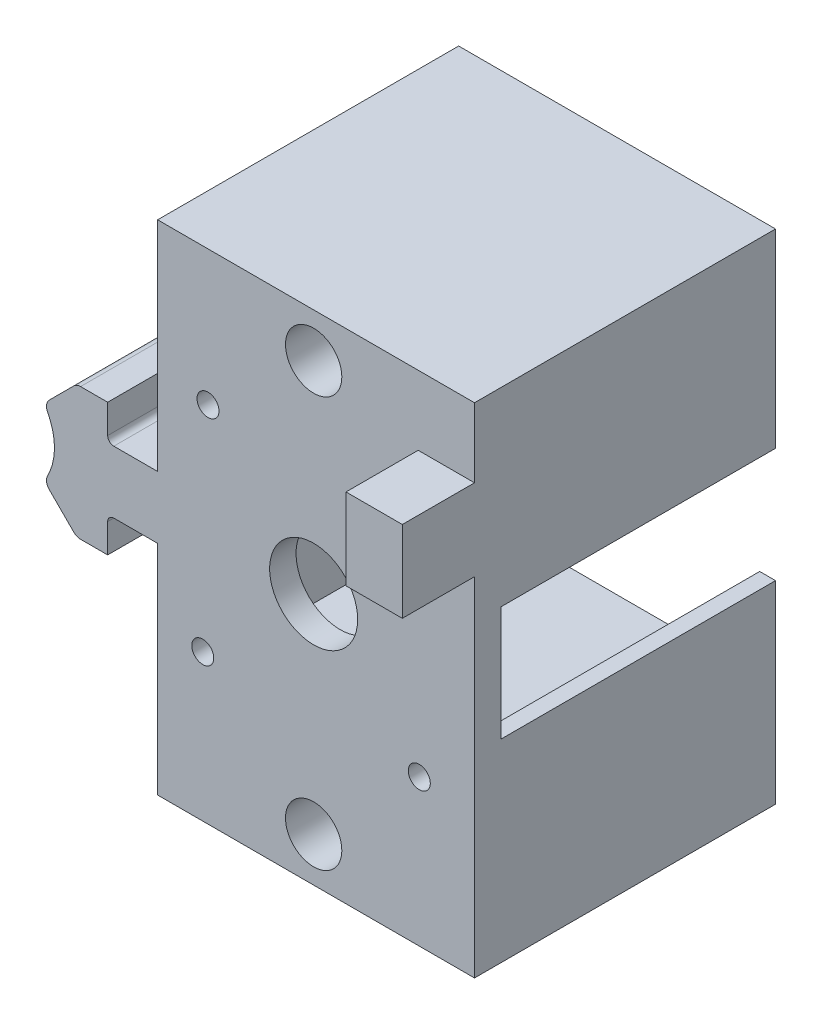
SolidWorks part; units mm, degrees
ref_plane "Front Plane" through (0, 0, 0) normal (0, 0, 1) x (1, 0, 0)
ref_plane "Top Plane" through (0, 0, 0) normal (0, 1, 0) x (1, 0, 0)
ref_plane "Right Plane" through (0, 0, 0) normal (1, 0, 0) x (0, 0, -1)
sketch "Sketch2" plane through (0, 0, 816.4924) normal (0, 0, 1) x (1, 0, 0)
  line L0 (35.7501, 34.0976) -> (35.7501, 33.2853)
  line L27 (48.1133, 38.1834) -> (50.6533, 38.1834)
  line L28 (50.6533, 38.1834) -> (50.6533, 56.9324)
  line L29 (50.6533, 56.9324) -> (52.6853, 56.9324)
  line L30 (52.6853, 56.9324) -> (52.6853, 10.4504)
  line L31 (52.6853, 10.4504) -> (50.6533, 10.4504)
  line L32 (50.6533, 10.4504) -> (50.6533, 29.1994)
  line L33 (50.6533, 29.1994) -> (48.1133, 29.1994)
  line L37 (44.3288, 29.1994) -> (48.1133, 29.1994)
  line L38 (43.4438, 24.1494) -> (43.4438, 28.3144)
  line L39 (39.5326, 24.1494) -> (43.4438, 24.1494)
  line L40 (35.016, 28.0957) -> (38.5589, 24.5527)
  line L41 (35.4657, 33.6914) -> (35.7501, 33.2853)
  line L42 (35.7501, 34.0976) -> (35.4657, 33.6914)
  line L43 (38.5589, 42.8301) -> (35.016, 39.2872)
  line L44 (43.4438, 43.2334) -> (39.5326, 43.2334)
  line L45 (43.4438, 39.0684) -> (43.4438, 43.2334)
  line L46 (48.1133, 38.1834) -> (44.3288, 38.1834)
  line L47 (44.3288, 29.1994) -> (48.1133, 29.1994)
  line L48 (43.4438, 24.1494) -> (43.4438, 28.3144)
  line L49 (39.5326, 24.1494) -> (43.4438, 24.1494)
  line L50 (35.016, 28.0957) -> (38.5589, 24.5527)
  line L53 (38.5589, 42.8301) -> (35.016, 39.2872)
  line L54 (43.4438, 43.2334) -> (39.5326, 43.2334)
  line L55 (43.4438, 39.0684) -> (43.4438, 43.2334)
  line L56 (48.1133, 38.1834) -> (44.3288, 38.1834)
  arc A38 (44.3288, 29.1994) -> (43.4438, 28.3144) centre (44.3288, 28.3144) ccw
  arc A39 (38.5589, 24.5527) -> (39.5326, 24.1494) centre (39.5326, 25.5264) ccw
  arc A40 (34.7724, 29.7132) -> (35.016, 28.0957) centre (35.9896, 29.0694) ccw
  arc A41 (34.7724, 29.7132) -> (35.7501, 33.2853) centre (27.2518, 33.6914) ccw
  arc A42 (35.7501, 34.0976) -> (34.7724, 37.6696) centre (27.2518, 33.6914) ccw
  arc A43 (35.016, 39.2872) -> (34.7724, 37.6696) centre (35.9896, 38.3135) ccw
  arc A44 (39.5326, 43.2334) -> (38.5589, 42.8301) centre (39.5326, 41.8564) ccw
  arc A45 (43.4438, 39.0684) -> (44.3288, 38.1834) centre (44.3288, 39.0684) ccw
  arc A46 (44.3288, 29.1994) -> (43.4438, 28.3144) centre (44.3288, 28.3144) ccw
  arc A47 (38.5589, 24.5527) -> (39.5326, 24.1494) centre (39.5326, 25.5264) ccw
  arc A48 (34.7724, 29.7132) -> (35.016, 28.0957) centre (35.9896, 29.0694) ccw
  arc A49 (34.7724, 29.7132) -> (35.7501, 33.2853) centre (27.2518, 33.6914) ccw
  arc A50 (35.7501, 34.0976) -> (34.7724, 37.6696) centre (27.2518, 33.6914) ccw
  arc A51 (35.016, 39.2872) -> (34.7724, 37.6696) centre (35.9896, 38.3135) ccw
  arc A52 (39.5326, 43.2334) -> (38.5589, 42.8301) centre (39.5326, 41.8564) ccw
  arc A53 (43.4438, 39.0684) -> (44.3288, 38.1834) centre (44.3288, 39.0684) ccw
  dimension "D2" = 46.482
  dimension "D3" = 2.032
  dimension "D4" = 2.54
  dimension "D1" = 0.508
extrude "Boss-Extrude1" add sketch "Sketch2" along normal blind 43.434
sketch "Sketch3" plane through (52.6853, 0, 0) normal (1, 0, 0) x (0, 0, -1)
  line L0 (-859.9264, 10.4504) -> (-816.4924, 10.4504) construction
  line L1 (-859.9264, 56.9324) -> (-856.1164, 56.9324)
  line L2 (-859.9264, 56.9324) -> (-859.9264, 10.4504)
  line L3 (-859.9264, 10.4504) -> (-856.1164, 10.4504)
  line L4 (-856.1164, 56.9324) -> (-856.1164, 10.4504)
  dimension "D1" = 3.81
extrude "Boss-Extrude2" add sketch "Sketch3" along normal blind 43.688
sketch "Sketch8" plane through (0, 0, 856.1164) normal (0, 0, -1) x (-1, 0, 0)
  line L0 (-52.6853, 10.4504) -> (-52.6853, 56.9324) construction
  line L1 (-96.3733, 56.9324) -> (-52.6853, 56.9324)
  line L2 (-96.3733, 56.9324) -> (-96.3733, 54.9004)
  line L3 (-94.0873, 54.9004) -> (-52.6853, 54.9004)
  line L4 (-52.6853, 56.9324) -> (-52.6853, 54.9004)
  line L6 (-96.3733, 10.4504) -> (-52.6853, 10.4504)
  line L7 (-96.3733, 10.4504) -> (-96.3733, 12.4824)
  line L8 (-94.0873, 12.4824) -> (-52.6853, 12.4824)
  line L9 (-52.6853, 10.4504) -> (-52.6853, 12.4824)
  line L11 (-96.3733, 54.9004) -> (-96.3733, 42.2204)
  line L12 (-96.3733, 42.2204) -> (-94.0873, 42.2204)
  line L13 (-94.0873, 54.9004) -> (-94.0873, 42.2204)
  line L15 (-96.3733, 12.4824) -> (-96.3733, 25.6904)
  line L16 (-96.3733, 25.6904) -> (-94.0873, 25.6904)
  line L17 (-94.0873, 12.4824) -> (-94.0873, 25.6904)
  dimension "D1" = 2.032
  dimension "D2" = 15.24
  dimension "D3" = 12.6801
  dimension "D5" = 2.286
  dimension "D6" = 2.032
extrude "Boss-Extrude5" add sketch "Sketch8" along direction (0, 0, 1) on the side of the normal up to surface (39.624 mm away)
sketch "Sketch9" plane through (0, 0, 859.9264) normal (0, 0, 1) x (1, 0, 0)
  circle A0 centre (73.1637, 34.1253) radius 6.35
  dimension "D1" = 12.7
extrude "Cut-Extrude1" cut sketch "Sketch9" against normal through all
sketch "Sketch10" plane through (0, 0, 856.1164) normal (0, 0, -1) x (-1, 0, 0)
  circle A0 centre (-89.1637, 50.1249) radius 1.5875
  circle A1 centre (-57.9217, 50.1464) radius 1.5875
  circle A2 centre (-57.1637, 18.9044) radius 1.5875
  circle A3 centre (-88.4057, 18.8829) radius 1.5875
  dimension "D1" = 3.175
  dimension "D2" = 31.242
  dimension "D3" = 31.242
  dimension "D4" = 31.242
  dimension "D5" = 31.242
extrude "Cut-Extrude2" cut sketch "Sketch10" against normal through all
sketch "Sketch12" plane through (0, 56.9324, 0) normal (0, 1, 0) x (1, 0, 0)
  line L1 (96.3733, -859.9264) -> (50.6533, -859.9264)
  line L2 (96.3733, -859.9264) -> (96.3733, -816.4924)
  line L3 (96.3733, -816.4924) -> (50.6533, -816.4924)
  line L4 (50.6533, -859.9264) -> (50.6533, -816.4924)
extrude "Boss-Extrude6" add sketch "Sketch12" along normal blind 12.7
sketch "Sketch13" plane through (0, 10.4504, 0) normal (0, -1, 0) x (1, 0, 0)
  line L1 (50.6533, 859.9264) -> (96.3733, 859.9264)
  line L2 (50.6533, 859.9264) -> (50.6533, 816.4924)
  line L3 (50.6533, 816.4924) -> (96.3733, 816.4924)
  line L4 (96.3733, 859.9264) -> (96.3733, 816.4924)
extrude "Boss-Extrude7" add sketch "Sketch13" along normal blind 12.7
sketch "Sketch14" plane through (0, 0, 859.9264) normal (0, 0, 1) x (1, 0, 0)
  line L0 (73.1637, 40.4753) -> (73.1637, 27.7753) construction
  line L1 (50.6533, 69.6324) -> (96.3733, 69.6324) construction
  line L2 (96.3733, -2.2496) -> (50.6533, -2.2496) construction
  line L3 (66.8137, 34.1253) -> (79.5137, 34.1253) construction
  circle A0 centre (73.1637, 63.2824) radius 4.064
  circle A1 centre (73.1637, 4.1004) radius 4.064
  circle A2 centre (73.1637, 34.1253) radius 6.35 construction
  point P16 (73.1637, 34.1253)
  dimension "D3" = 8.128
  dimension "D1" = 6.35
  dimension "D2" = 6.35
extrude "Cut-Extrude3" cut sketch "Sketch14" against normal blind 6.35
sketch "Sketch15" plane through (0, 0, 859.9264) normal (0, 0, 1) x (1, 0, 0)
  line L0 (96.3733, 69.6324) -> (96.3733, -2.2496) construction
  line L1 (88.2459, 59.6283) -> (96.3733, 59.6283)
  line L2 (88.2459, 59.6283) -> (88.2459, 47.8989)
  line L3 (88.2459, 47.8989) -> (96.3733, 47.8989)
  line L4 (96.3733, 59.6283) -> (96.3733, 47.8989)
extrude "Boss-Extrude8" add sketch "Sketch15" along normal blind 10.414
